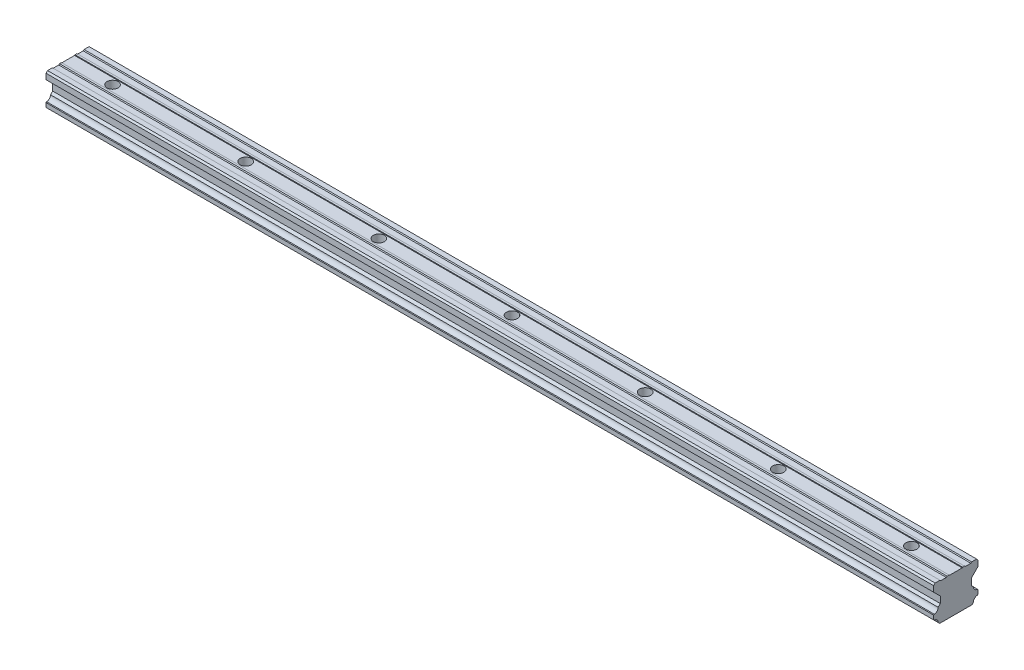
SolidWorks part; units mm, degrees
material "AISI 1020 Steel, Cold Rolled"
ref_plane "Front Plane" through (0, 0, 0) normal (0, 0, 1) x (1, 0, 0)
ref_plane "Top Plane" through (0, 0, 0) normal (0, 1, 0) x (1, 0, 0)
ref_plane "Right Plane" through (0, 0, 0) normal (1, 0, 0) x (0, 0, -1)
sketch "Sketch1" plane through (0, 0, 0) normal (1, 0, 0) x (0, 0, -1)
  line L0 (-7.9658, -7.694) -> (-7.2663, -8.3935)
  line L1 (-7.2663, -8.3935) -> (7.2663, -8.3935)
  line L2 (7.2663, -8.3935) -> (7.9658, -7.694)
  line L3 (9.7474, -5.9133) -> (10, -5.6608)
  line L4 (10, -5.6608) -> (10, -3.7884)
  line L5 (10, -3.7884) -> (9.7474, -3.5358)
  line L6 (7.9658, -1.7232) -> (7.0051, -0.7626)
  line L7 (7.0051, -0.7626) -> (7.0051, 2.1662)
  line L8 (7.0051, 2.1662) -> (10, 5.1611)
  line L9 (10, 5.1611) -> (10, 7.7124)
  line L10 (10, 7.7124) -> (9.4085, 8.3935)
  line L11 (9.4085, 8.3935) -> (7.133, 8.3935)
  line L12 (7.133, 8.3935) -> (6.7895, 8.05)
  line L13 (6.7895, 8.05) -> (4.2711, 8.05)
  line L14 (4.2711, 8.05) -> (3.9277, 8.3935)
  line L15 (3.9277, 8.3935) -> (3.0613, 8.3935)
  line L16 (3.0613, 8.3935) -> (2.872, 8.2042)
  line L17 (2.872, 8.2042) -> (-2.872, 8.2042)
  line L18 (-2.872, 8.2042) -> (-3.0613, 8.3935)
  line L19 (-3.0613, 8.3935) -> (-3.9277, 8.3935)
  line L20 (-3.9277, 8.3935) -> (-4.2712, 8.05)
  line L21 (-4.2712, 8.05) -> (-6.7895, 8.05)
  line L22 (-6.7895, 8.05) -> (-7.133, 8.3935)
  line L23 (-7.133, 8.3935) -> (-9.3077, 8.3935)
  line L24 (-9.3077, 8.3935) -> (-10, 7.7012)
  line L25 (-10, 7.7012) -> (-10, 5.1611)
  line L26 (-10, 5.1611) -> (-7.0051, 2.1662)
  line L27 (-7.0051, 2.1662) -> (-7.0051, -0.7626)
  line L28 (-7.0051, -0.7626) -> (-7.9658, -1.7232)
  line L29 (-9.7474, -5.9133) -> (-10, -5.6608)
  line L30 (-10, -5.6608) -> (-10, -3.7884)
  line L31 (-10, -3.7884) -> (-9.7474, -3.5358)
  arc A0 (-7.9658, -7.694) -> (-9.7474, -5.9133) centre (-9.7035, -7.6511) ccw
  arc A1 (-9.7474, -3.5358) -> (-7.9658, -1.7232) centre (-9.7025, -1.7981) ccw
  arc A2 (7.9658, -1.7232) -> (9.7474, -3.5358) centre (9.7025, -1.7981) ccw
  arc A3 (9.7474, -5.9133) -> (7.9658, -7.694) centre (9.7035, -7.6511) ccw
extrude "Boss-Extrude1" add sketch "Sketch1" along normal blind 400
sketch "Sketch2" plane through (0, -8.3935, 0) normal (0, -1, 0) x (1, 0, 0)
  circle A0 centre (20, 0) radius 3
  dimension "D1" = 6
  dimension "D2" = 20
hole_wizard "Hole1" positions "3DSketch1" profile "Sketch3" legacy end condition through all
sketch3d "3DSketch1"
  point P0 (20, -8.3935, 0)
sketch "Sketch3" plane through (20, -8.3935, 0) normal (1, 0, 0) x (0, 0, -1)
  line L0 (0, 0) -> (0, 16.7869)
  line L1 (0, 16.7869) -> (2.5, 16.7869)
  line L2 (2.5, 16.7869) -> (2.5, 8.5)
  line L3 (2.5, 8.5) -> (4.75, 8.5)
  line L4 (4.75, 8.5) -> (4.75, 0)
  line L5 (4.75, 0) -> (0, 0)
  line L6 (0, 110) -> (0, -10) construction
  dimension "Diameter" = 5
  dimension "Depth" = 16.7869
  dimension "C-Bore Diameter" = 9.5
  dimension "C-Bore Depth" = 8.5
sketch "Sketch4" plane through (0, -8.3935, 0) normal (0, -1, 0) x (-1, 0, 0)
  line L0 (0, 0) -> (-400, 0) construction
  line L1 (-400, -7.2663) -> (-400, 7.2663) construction
other "Move Face2" [suppressed] parameters "D1"=8.5
pattern_linear "LPattern1" count 7 spacing 60 along (1, 0, 0) of "Hole1"
pattern_linear "LPattern2" [suppressed] count 5 spacing 60
